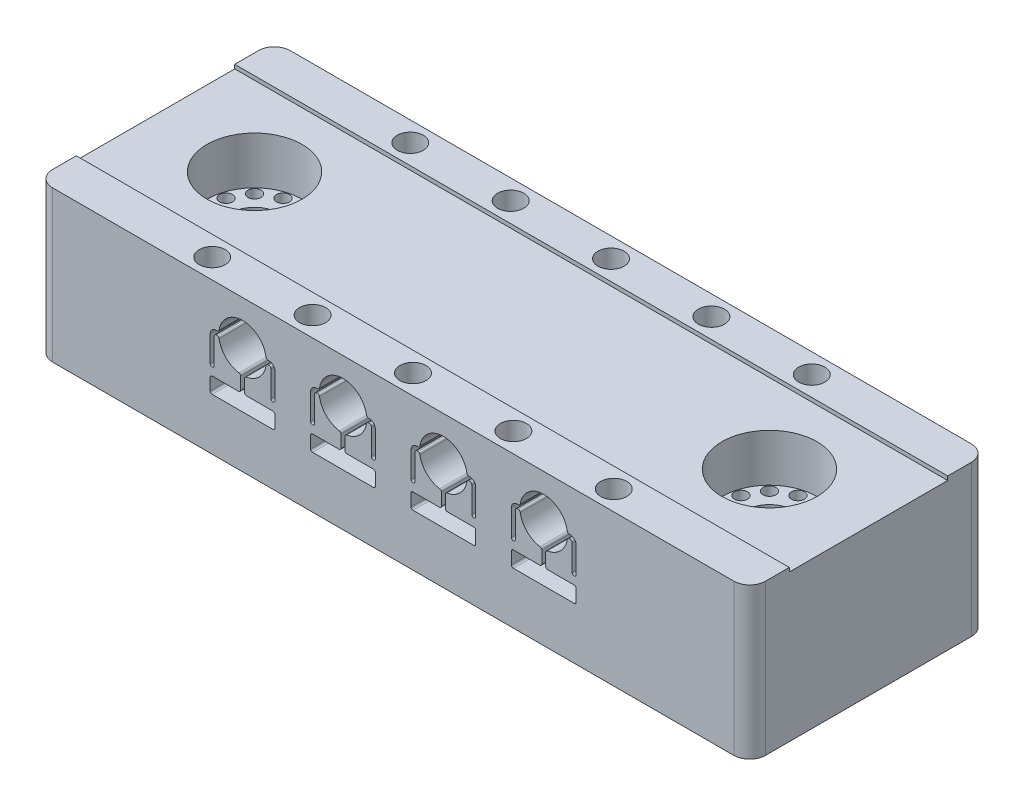
SolidWorks part; units mm, degrees
material "Plain Carbon Steel"
ref_plane "Front Plane" through (0, 0, 0) normal (0, 0, 1) x (1, 0, 0)
ref_plane "Top Plane" through (0, 0, 0) normal (0, 1, 0) x (1, 0, 0)
ref_plane "Right Plane" through (0, 0, 0) normal (1, 0, 0) x (0, 0, -1)
sketch "Sketch1" plane through (0, 0, 0) normal (0, 1, 0) x (1, 0, 0)
  line L0 (-45, 13) -> (-45, -13)
  line L3 (-43, -15) -> (43, -15)
  line L4 (45, -13) -> (45, 13)
  line L5 (43, 15) -> (-43, 15)
  line L6 (-32.5, 0) -> (32.5, 0) construction
  line L8 (-33.8159, 4.9109) -> (-36.095, 3.595) construction
  line L9 (-36.095, 3.595) -> (-37.4109, 1.3159) construction
  line L10 (-37.4109, 1.3159) -> (-37.4109, -1.3159) construction
  line L11 (-37.4109, -1.3159) -> (-36.095, -3.595) construction
  line L12 (-36.095, -3.595) -> (-33.8159, -4.9109) construction
  line L13 (-33.8159, -4.9109) -> (-31.1841, -4.9109) construction
  line L14 (-31.1841, -4.9109) -> (-28.905, -3.595) construction
  line L15 (-28.905, -3.595) -> (-27.5891, -1.3159) construction
  line L16 (-27.5891, -1.3159) -> (-27.5891, 1.3159) construction
  line L17 (-27.5891, 1.3159) -> (-28.905, 3.595) construction
  line L18 (-28.905, 3.595) -> (-31.1841, 4.9109) construction
  line L19 (-31.1841, 4.9109) -> (-33.8159, 4.9109) construction
  line L20 (33.8159, 4.9109) -> (31.1841, 4.9109) construction
  line L21 (31.1841, 4.9109) -> (28.905, 3.595) construction
  line L22 (28.905, 3.595) -> (27.5891, 1.3159) construction
  line L23 (27.5891, 1.3159) -> (27.5891, -1.3159) construction
  line L24 (27.5891, -1.3159) -> (28.905, -3.595) construction
  line L25 (28.905, -3.595) -> (31.1841, -4.9109) construction
  line L26 (31.1841, -4.9109) -> (33.8159, -4.9109) construction
  line L27 (33.8159, -4.9109) -> (36.095, -3.595) construction
  line L28 (36.095, -3.595) -> (37.4109, -1.3159) construction
  line L29 (37.4109, -1.3159) -> (37.4109, 1.3159) construction
  line L30 (37.4109, 1.3159) -> (36.095, 3.595) construction
  line L31 (36.095, 3.595) -> (33.8159, 4.9109) construction
  circle A2 centre (-32.5, 0) radius 3
  circle A3 centre (32.5, 0) radius 3
  circle A17 centre (32.5, 0) radius 6 construction
  circle A18 centre (-32.5, 0) radius 6 construction
  circle A19 centre (-31.1841, 4.9109) radius 0.9159 construction
  circle A20 centre (-31.1841, 4.9109) radius 0.8159
  circle A21 centre (-32.5, 0) radius 4.9109 construction
  circle A22 centre (-33.8159, 4.9109) radius 0.8159
  circle A23 centre (-33.8159, 4.9109) radius 1.8159 construction
  circle A24 centre (-36.095, 3.595) radius 0.8159
  circle A25 centre (-37.4109, 1.3159) radius 0.8159
  circle A26 centre (-37.4109, -1.3159) radius 0.8159
  circle A27 centre (-36.095, -3.595) radius 0.8159
  circle A28 centre (-33.8159, -4.9109) radius 0.8159
  circle A29 centre (-31.1841, -4.9109) radius 0.8159
  circle A30 centre (-28.905, -3.595) radius 0.8159
  circle A31 centre (-27.5891, -1.3159) radius 0.8159
  circle A32 centre (-27.5891, 1.3159) radius 0.8159
  circle A33 centre (-28.905, 3.595) radius 0.8159
  circle A34 centre (32.5, 0) radius 4.9109 construction
  circle A35 centre (31.1841, 4.9109) radius 0.8159
  circle A36 centre (33.8159, 4.9109) radius 0.8159
  circle A37 centre (36.095, 3.595) radius 0.8159
  circle A38 centre (37.4109, 1.3159) radius 0.8159
  circle A39 centre (37.4109, -1.3159) radius 0.8159
  circle A40 centre (36.095, -3.595) radius 0.8159
  circle A41 centre (33.8159, -4.9109) radius 0.8159
  circle A42 centre (31.1841, -4.9109) radius 0.8159
  circle A43 centre (28.905, -3.595) radius 0.8159
  circle A44 centre (27.5891, -1.3159) radius 0.8159
  circle A45 centre (27.5891, 1.3159) radius 0.8159
  circle A46 centre (28.905, 3.595) radius 0.8159
  arc A47 (43, -15) -> (45, -13) centre (43, -13) ccw
  arc A48 (-45, -13) -> (-43, -15) centre (-43, -13) ccw
  arc A49 (-45, 13) -> (-43, 15) centre (-43, 13) cw
  arc A50 (45, 13) -> (43, 15) centre (43, 13) ccw
  point P2 (-45, 0)
  point P6 (0, 15)
  point P72 (-45, 15)
  point P75 (45, 15)
  dimension "D1" = 90
  dimension "D2" = 12
  dimension "D3" = 65
  dimension "D4" = 6
  dimension "D5" = 30
  dimension "D6" = 0.1
  dimension "D7" = 1.6317
  dimension "D8" = 1
  dimension "D9" = 2
extrude "Boss-Extrude1" add sketch "Sketch1" along normal blind 19.05
sketch "Sketch2" plane through (0, 19.05, 0) normal (0, 1, 0) x (1, 0, 0)
  circle A0 centre (32.5, 0) radius 6 construction
  circle A1 centre (-32.5, 0) radius 6 construction
  circle A2 centre (32.5, 0) radius 6
  circle A3 centre (-32.5, 0) radius 6
extrude "Cut-Extrude1" cut sketch "Sketch2" against normal blind 6.5
sketch "Sketch3" plane through (0, 0, 15) normal (0, 0, 1) x (1, 0, 0)
  line L0 (0, 19.05) -> (0, 13.55) construction
  line L1 (-43, 19.05) -> (43, 19.05) construction
  line L2 (-22.2184, 13.8) -> (-22.3427, 13.8)
  line L3 (-22.2184, 13.3) -> (-22.3427, 13.3)
  line L4 (-23.0927, 13.05) -> (-23.0927, 9.8)
  line L5 (-22.5927, 13.05) -> (-22.5927, 9.8)
  line L6 (-15.7957, 13.8) -> (-15.6714, 13.8)
  line L7 (-15.7957, 13.3) -> (-15.6714, 13.3)
  line L8 (-15.4214, 13.05) -> (-15.4214, 9.8)
  line L9 (-14.9214, 13.05) -> (-14.9214, 9.8)
  line L10 (-19.257, 10.3387) -> (-19.257, 8.8)
  line L11 (-19.507, 8.55) -> (-22.8427, 8.55)
  line L12 (-18.757, 10.3387) -> (-18.757, 8.8)
  line L13 (-18.507, 8.55) -> (-15.1714, 8.55)
  line L14 (-22.8427, 6.5478) -> (-15.1714, 6.5478)
  line L15 (-23.0927, 8.3) -> (-23.0927, 6.7978)
  line L16 (-14.9214, 8.3) -> (-14.9214, 6.7978)
  line L17 (-19.007, 16.55) -> (-19.007, 19.05) construction
  line L18 (-22.2184, 13.3) -> (-22.2184, 13.8) construction
  line L19 (-22.8427, 9.55) -> (-22.8427, 8.55) construction
  line L20 (-19.257, 10.3387) -> (-18.757, 10.3387) construction
  line L21 (-21.507, 6.5478) -> (-21.507, 0) construction
  line L22 (-43, 0) -> (43, 0) construction
  line L23 (-16.507, 6.5478) -> (-16.507, 0) construction
  line L24 (-21.507, 3.2739) -> (-16.507, 3.2739) construction
  line L25 (-19.007, 3.2739) -> (-19.007, 6.5478) construction
  line L26 (-19.007, 8.55) -> (-19.007, 10.55) construction
  line L27 (-21.507, 6.5478) -> (-19.007, 8.05) construction
  line L28 (-19.007, 8.05) -> (-16.507, 6.5478) construction
  line L29 (-19.007, 13.55) -> (-14.9214, 13.55) construction
  line L30 (-14.9214, 13.55) -> (-10.4214, 13.55) construction
  line L31 (-10.4214, 13.55) -> (-6.3357, 13.55) construction
  line L32 (-6.3357, 13.55) -> (-2.25, 13.55) construction
  line L33 (-2.25, 13.55) -> (2.25, 13.55) construction
  line L34 (2.25, 13.55) -> (6.3357, 13.55) construction
  line L35 (6.3357, 13.55) -> (10.4214, 13.55) construction
  line L36 (10.4214, 13.55) -> (14.9214, 13.55) construction
  line L37 (14.9214, 13.55) -> (19.007, 13.55) construction
  arc A0 (-21.9713, 13.0885) -> (-19.4686, 10.5857) centre (-19.007, 13.55) ccw
  arc A1 (-22.3427, 13.8) -> (-23.0927, 13.05) centre (-22.3427, 13.05) ccw
  arc A2 (-22.3427, 13.3) -> (-22.5927, 13.05) centre (-22.3427, 13.05) ccw
  arc A3 (-23.0927, 9.8) -> (-22.5927, 9.8) centre (-22.8427, 9.8) ccw
  arc A4 (-15.6714, 13.8) -> (-14.9214, 13.05) centre (-15.6714, 13.05) cw
  arc A5 (-15.6714, 13.3) -> (-15.4214, 13.05) centre (-15.6714, 13.05) cw
  arc A6 (-15.4214, 9.8) -> (-14.9214, 9.8) centre (-15.1714, 9.8) ccw
  arc A7 (-16.0428, 14.0115) -> (-21.9713, 14.0115) centre (-19.007, 13.55) ccw
  arc A8 (-15.7957, 13.8) -> (-16.0428, 14.0115) centre (-15.7957, 14.05) cw
  arc A9 (-15.7957, 13.3) -> (-16.0428, 13.0885) centre (-15.7957, 13.05) ccw
  arc A10 (-22.2184, 13.3) -> (-21.9713, 13.0885) centre (-22.2184, 13.05) cw
  arc A11 (-22.2184, 13.8) -> (-21.9713, 14.0115) centre (-22.2184, 14.05) ccw
  arc A12 (-18.5455, 10.5857) -> (-16.0428, 13.0885) centre (-19.007, 13.55) ccw
  arc A13 (-19.257, 8.8) -> (-19.507, 8.55) centre (-19.507, 8.8) cw
  arc A14 (-22.8427, 8.55) -> (-23.0927, 8.3) centre (-22.8427, 8.3) ccw
  arc A15 (-23.0927, 6.7978) -> (-22.8427, 6.5478) centre (-22.8427, 6.7978) ccw
  arc A16 (-14.9214, 6.7978) -> (-15.1714, 6.5478) centre (-15.1714, 6.7978) cw
  arc A17 (-15.1714, 8.55) -> (-14.9214, 8.3) centre (-15.1714, 8.3) cw
  arc A18 (-18.757, 8.8) -> (-18.507, 8.55) centre (-18.507, 8.8) ccw
  arc A19 (-18.757, 10.3387) -> (-18.5455, 10.5857) centre (-18.507, 10.3387) cw
  arc A20 (-19.257, 10.3387) -> (-19.4686, 10.5857) centre (-19.507, 10.3387) ccw
  point P30 (-16.0175, 13.8)
  point P59 (-18.757, 10.5604)
  dimension "D1" = 2.5
  dimension "D2" = 1
  dimension "D5" = 3
  dimension "D3" = 0.5
  dimension "D4" = 5
  dimension "D6" = 2
  dimension "D7" = 118
  dimension "D8" = 0.5
  dimension "D9" = 4.0857
  dimension "D10" = 4.5
extrude "Cut-Extrude2" cut sketch "Sketch3" against normal through all
pattern_linear "LPattern1" count 4 spacing 12.6714 along (1, 0, 0) of "Cut-Extrude2"
sketch "Sketch4" plane through (0, 19.05, 0) normal (0, 1, 0) x (1, 0, 0)
  line L0 (-45, -10) -> (45, -10)
  line L1 (-45, 13) -> (-45, -13) construction
  line L2 (45, -13) -> (45, 13) construction
  line L3 (45, -10) -> (45, 10)
  line L4 (45, 10) -> (-45, 10)
  line L5 (-45, 10) -> (-45, -10)
  line L6 (10.4214, -15) -> (14.9214, -15) construction
  line L7 (-2.25, -15) -> (2.25, -15) construction
  line L8 (-14.9214, -15) -> (-10.4214, -15) construction
  line L9 (10.4214, -15) -> (14.9214, -15) construction
  line L10 (-2.25, -15) -> (2.25, -15) construction
  line L11 (-14.9214, -15) -> (-10.4214, -15) construction
  line L12 (-14.9214, -15) -> (-23.0927, -15) construction
  line L13 (-43, -15) -> (43, -15) construction
  line L14 (-23.0927, -15) -> (-27.5927, -15) construction
  line L15 (-10.4214, -15) -> (-2.25, -15) construction
  line L16 (-25.3427, -15) -> (-25.3427, -10) construction
  line L17 (-25.3427, 10) -> (-25.3427, 15) construction
  line L18 (43, 15) -> (-43, 15) construction
  line L20 (14.9214, -15) -> (23.0927, -15) construction
  line L21 (23.0927, -15) -> (27.5927, -15) construction
  line L22 (25.3427, -15) -> (25.3427, -10) construction
  circle A0 centre (-25.3427, -12.5) radius 2.5 construction
  circle A1 centre (-25.3427, -12.5) radius 2 construction
  circle A2 centre (-25.3427, 12.5) radius 2.5 construction
  circle A3 centre (-25.3427, 12.5) radius 2 construction
  point P9 (-45, 0)
  point P21 (25.3427, -12.5)
  dimension "D1" = 0.5
  dimension "D2" = 4
sketch "Sketch5" plane through (0, 19.05, 0) normal (0, 1, 0) x (1, 0, 0)
  point P0 (-25.3427, -12.5)
  point P3 (-25.3427, 12.5)
hole_wizard "M4x0.7 Tapped Hole1" positions "Sketch5" profile "Sketch6" tap size "M4x0.7" standard "ANSI Metric"
sketch "Sketch6" plane through (-25.3427, 19.05, 12.5) normal (1, 0, 0) x (0, 0, 1)
  line L0 (0, 0) -> (0, 11.0914)
  line L1 (0, 11.0914) -> (1.65, 10.1)
  line L2 (1.65, 10.1) -> (1.65, 0)
  line L5 (1.65, 0) -> (0, 0)
  line L10 (0, 11.0914) -> (-1.65, 10.1) construction
  line L11 (0, -6.35) -> (0, 107.95) construction
  dimension "Tap Drill Dia." = 3.3
  dimension "Tap Drill Depth" = 10.1
  dimension "Drill Angle" = 118
cosmetic thread "Hole Thread1" parameters "D1"=8, "D2"=4
cosmetic thread "Hole Thread2" parameters "D1"=8, "D2"=4
pattern_linear "LPattern2" count 5 spacing 12.6714 along (1, 0, 0) of "M4x0.7 Tapped Hole1"
cosmetic thread "Hole Thread3" parameters "D1"=8, "D2"=4
cosmetic thread "Hole Thread4" parameters "D1"=8, "D2"=4
cosmetic thread "Hole Thread5" parameters "D1"=8, "D2"=4
cosmetic thread "Hole Thread6" parameters "D1"=8, "D2"=4
cosmetic thread "Hole Thread7" parameters "D1"=8, "D2"=4
cosmetic thread "Hole Thread8" parameters "D1"=8, "D2"=4
cosmetic thread "Hole Thread9" parameters "D1"=8, "D2"=4
cosmetic thread "Hole Thread10" parameters "D1"=8, "D2"=4
extrude "Cut-Extrude3" cut sketch "Sketch4" against normal blind 0.5
sketch "Sketch7" plane through (0, 0, 0) normal (0, -1, 0) x (1, 0, 0)
  line L0 (-22.8427, 15) -> (-15.1714, 15) construction
  line L1 (-22.8427, 15) -> (-15.1714, 15) construction
  line L2 (15.1714, 15) -> (22.8427, 15) construction
  line L3 (15.1714, 15) -> (22.8427, 15) construction
  line L4 (-19.007, 5) -> (-19.007, -5) construction
  circle A0 centre (-19.007, 5) radius 2.5
  circle A1 centre (-19.007, -5) radius 2.5
  point P6 (-19.007, 15)
  point P7 (19.007, 15)
  point P8 (-19.007, 0)
  dimension "D2" = 5
  dimension "D1" = 10
extrude "Cut-Extrude4" cut sketch "Sketch7" against normal up to surface (6.5478 mm away)
pattern_linear "LPattern3" count 4 spacing 12.6714 along (1, 0, 0) of "Cut-Extrude4"
